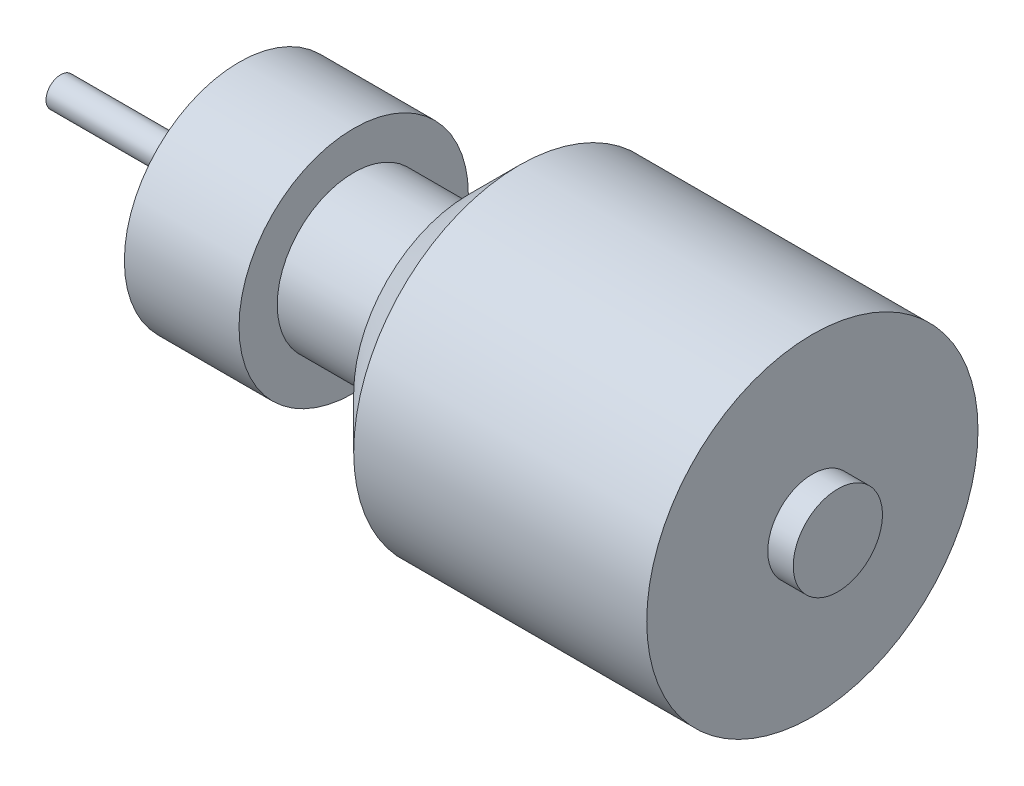
SolidWorks part; units mm, degrees
ref_plane "Plan de face" through (0, 0, 0) normal (0, 0, 1) x (1, 0, 0)
ref_plane "Plan de dessus" through (0, 0, 0) normal (0, 1, 0) x (1, 0, 0)
ref_plane "Plan de droite" through (0, 0, 0) normal (1, 0, 0) x (0, 0, -1)
sketch "Esquisse1" plane through (0, 0, 0) normal (0, 0, 1) x (1, 0, 0)
  line L0 (-25.8801, 0) -> (62.5792, 0) construction
  line L1 (-14, 1.15) -> (0, 1.15)
  line L2 (0, 1.15) -> (0, 9)
  line L3 (0, 9) -> (9, 9)
  line L4 (9, 9) -> (9, 6)
  line L5 (9, 6) -> (18, 6)
  line L6 (18, 6) -> (18, 9)
  line L7 (18, 9) -> (22, 13)
  line L8 (22, 13) -> (45, 13)
  line L9 (45, 13) -> (45, 3.5)
  line L10 (45, 3.5) -> (47, 3.5)
  line L11 (47, 3.5) -> (47, 0)
  line L12 (47, 0) -> (-14, 0)
  line L13 (-14, 0) -> (-14, 1.15)
  dimension "D1" = 2.3
  dimension "D2" = 47
  dimension "D3" = 26
  dimension "D4" = 14
  dimension "D5" = 18
  dimension "D6" = 9
  dimension "D7" = 9
  dimension "D8" = 2
  dimension "D9" = 7
  dimension "D10" = 12
  dimension "D11" = 45
  dimension "D12" = 3
revolve "Révolution1" add sketch "Esquisse1" angle 360 about L0
hole_wizard "Trou taraudé M2x0.41" positions "Esquisse3" profile "Esquisse2" tap size "M2x0.4" standard "Ansi Metric"
sketch "Esquisse3" plane through (0, 0, 0) normal (-1, 0, 0) x (0, 0, 1)
  circle A0 centre (0, 0) radius 5.1649 construction
  point P0 (0, 5.1649)
  point P2 (5.1649, 0)
  point P4 (0, -5.1649)
  point P6 (-5.1649, 0)
sketch "Esquisse2" plane through (0, 5.1649, 0) normal (0, 1, 0) x (0, 0, 1)
  line L0 (0, 0) -> (0, 6.4807)
  line L1 (0, 6.4807) -> (0.8, 6)
  line L2 (0.8, 6) -> (0.8, 0.225)
  line L3 (0.8, 0.225) -> (1.025, 0)
  line L5 (1.025, 0) -> (0, 0)
  line L6 (-0.8, 0.225) -> (-1.025, 0) construction
  line L10 (0, 6.4807) -> (-0.8, 6) construction
  line L11 (0, -6.35) -> (0, 107.95) construction
  dimension "Diamètre du trou pour taraudage" = 1.6
  dimension "Profondeur du trou pour taraudage" = 6
  dimension "Diamètre du fraisage entrant" = 2.05
  dimension "Angle du fraisage entrant" = 90
  dimension "Angle de pointe" = 118
cosmetic thread "Filetage de perçage1" parameters "D1"=4, "D2"=2
cosmetic thread "Filetage de perçage2" parameters "D1"=4, "D2"=2
cosmetic thread "Filetage de perçage3" parameters "D1"=4, "D2"=2
cosmetic thread "Filetage de perçage4" parameters "D1"=4, "D2"=2
